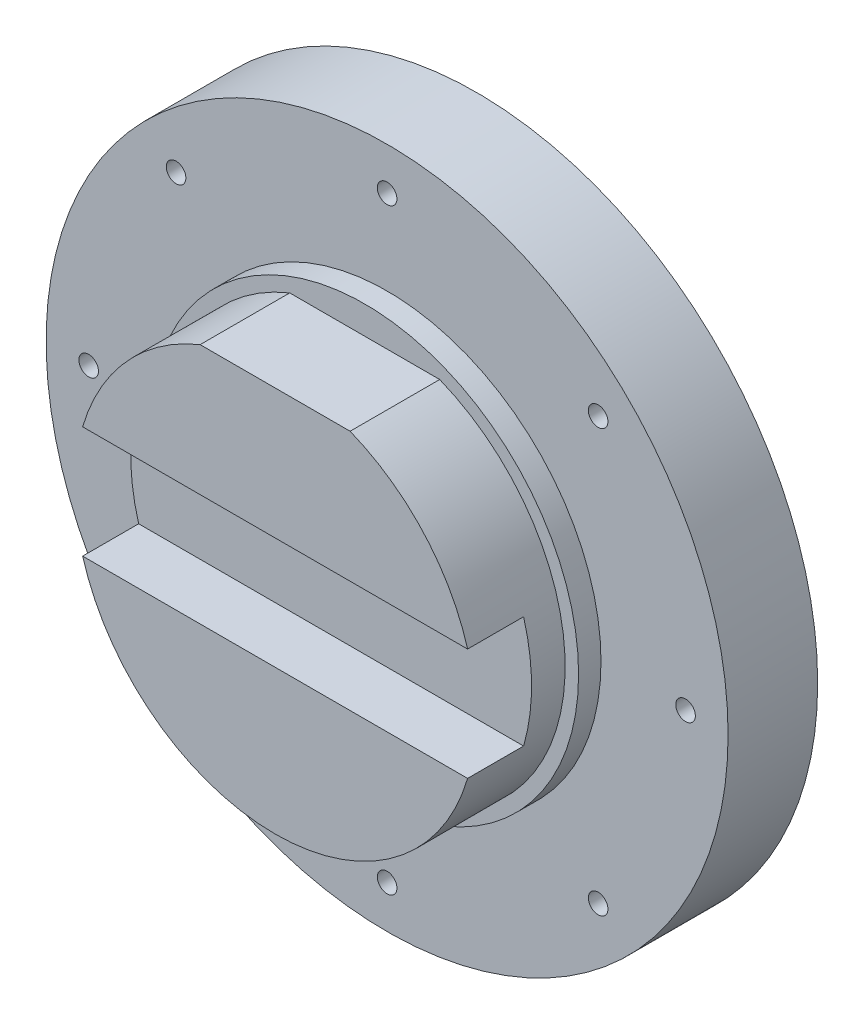
SolidWorks part; units mm, degrees
ref_plane "Front Plane" through (0, 0, 0) normal (0, 0, 1) x (1, 0, 0)
ref_plane "Top Plane" through (0, 0, 0) normal (0, 1, 0) x (1, 0, 0)
ref_plane "Right Plane" through (0, 0, 0) normal (1, 0, 0) x (0, 0, -1)
sketch "Sketch1" plane through (0, 0, 0) normal (0, 0, 1) x (1, 0, 0)
  line L0 (0, 0) -> (0, 166) construction
  line L1 (-66.9701, 166) -> (66.9701, 166)
  line L2 (0, -304.5) -> (0, 399.1699) construction
  circle A0 centre (0, 0) radius 304.5
  circle A1 centre (0, 0) radius 266.5
  circle A2 centre (0, 0) radius 191
  arc A3 (-66.9701, 166) -> (66.9701, 166) centre (0, 0) ccw
  point P10 (0, 166)
  dimension "D1" = 609
  dimension "D2" = 533
  dimension "D3" = 382
  dimension "D4" = 358
  dimension "D5" = 166
extrude "Boss-Extrude2" add sketch "Sketch1" along normal blind 80 contours A0 A1 | A1 A2
sketch "Sketch2" plane through (0, 0, 80) normal (0, 0, 1) x (1, 0, 0)
  line L0 (0, 0) -> (0, 166)
  line L1 (-66.9701, 166) -> (66.9701, 166)
  arc A0 (-66.9701, 166) -> (66.9701, 166) centre (0, 0) ccw
  point P7 (0, 166)
  circle M3 centre (0, 0) radius 191
  dimension "D1" = 358
  dimension "D2" = 166
extrude "Boss-Extrude3" add sketch "Sketch2" along normal blind 20 separate body contours A0 L1 M3
sketch "Sketch3" plane through (0, 0, 100) normal (0, 0, 1) x (1, 0, 0)
  line L0 (-66.9701, 166) -> (66.9701, 166)
  arc A0 (-66.9701, 166) -> (66.9701, 166) centre (0, 0) ccw
extrude "Boss-Extrude4" add sketch "Sketch3" along normal blind 80 separate body
sketch "Sketch4" plane through (0, 0, 180) normal (0, 0, 1) x (1, 0, 0)
  line L1 (-184.3394, 50) -> (184.3394, 50)
  line L2 (-184.3394, 50) -> (-184.3394, -50)
  line L3 (-184.3394, -50) -> (184.3394, -50)
  line L4 (184.3394, 50) -> (184.3394, -50)
  line L5 (-184.3394, 50) -> (184.3394, -50) construction
  line L6 (-184.3394, -50) -> (184.3394, 50) construction
  circle A0 centre (0, 0) radius 191 construction
  point P0 (0, 0)
  dimension "D1" = 100
extrude "Cut-Extrude1" cut sketch "Sketch4" against normal blind 50
sketch "Sketch5" plane through (0, 0, 180) normal (0, 0, 1) x (1, 0, 0)
  line L0 (0, 0) -> (0, 565.5999) construction
  circle A0 centre (0, 0) radius 266.5
  arc A1 (0, 266.5) -> (-188.4417, 188.4462) centre (0, 0) ccw
  circle A2 centre (-188.4417, 188.4462) radius 8.75
  arc A3 (-188.4417, 188.4462) -> (-132, 231.513) centre (0, 0) ccw
  arc A5 (-132, 231.513) -> (-182.4593, 194.2443) centre (0, 0) ccw
  arc A6 (0, 266.5) -> (-188.4417, 188.4462) centre (0, 0) ccw
  arc A7 (-188.4417, 188.4462) -> (-266.5, 0) centre (0, 0) ccw
  circle A8 centre (-266.5, 0) radius 8.75
  arc A9 (-266.5, 0) -> (-188.4417, -188.4462) centre (0, 0) ccw
  circle A10 centre (-188.4417, -188.4462) radius 8.75
  arc A11 (-188.4417, -188.4462) -> (0, -266.5) centre (0, 0) ccw
  circle A12 centre (0, -266.5) radius 8.75
  circle A13 centre (188.4417, -188.4462) radius 8.75
  circle A14 centre (266.5, 0) radius 8.75
  circle A15 centre (188.4417, 188.4462) radius 8.75
  circle A16 centre (0, 266.5) radius 8.75
  dimension "D1" = 533
  dimension "D2" = 132
  dimension "D3" = 17.5
  dimension "D4" = 188.4417
  dimension "D5" = 17.5
  dimension "D6" = 17.5
  dimension "D7" = 17.5
  dimension "D8" = 17.5
extrude "Cut-Extrude2" cut sketch "Sketch5" against normal blind 130 contours A15 | A16 | A2 | A8 | A10 | A12 | A13 | A14
